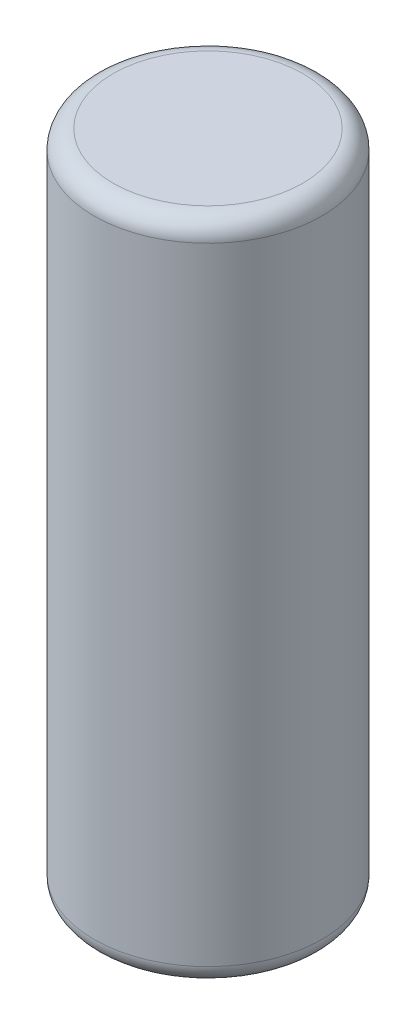
SolidWorks part; units mm, degrees
material "Cast Alloy Steel"
ref_plane "Front Plane" through (0, 0, 0) normal (0, 0, 1) x (1, 0, 0)
ref_plane "Top Plane" through (0, 0, 0) normal (0, 1, 0) x (1, 0, 0)
ref_plane "Right Plane" through (0, 0, 0) normal (1, 0, 0) x (0, 0, -1)
sketch "Sketch1" plane through (0, 0, 0) normal (0, 1, 0) x (1, 0, 0)
  circle A0 centre (0, 0) radius 6
  dimension "D1" = 12
extrude "Boss-Extrude1" add sketch "Sketch1" along normal blind 35
fillet "Fillet1" radius 1 2 edges at (0, 0, 6) (0, 35, 6)
